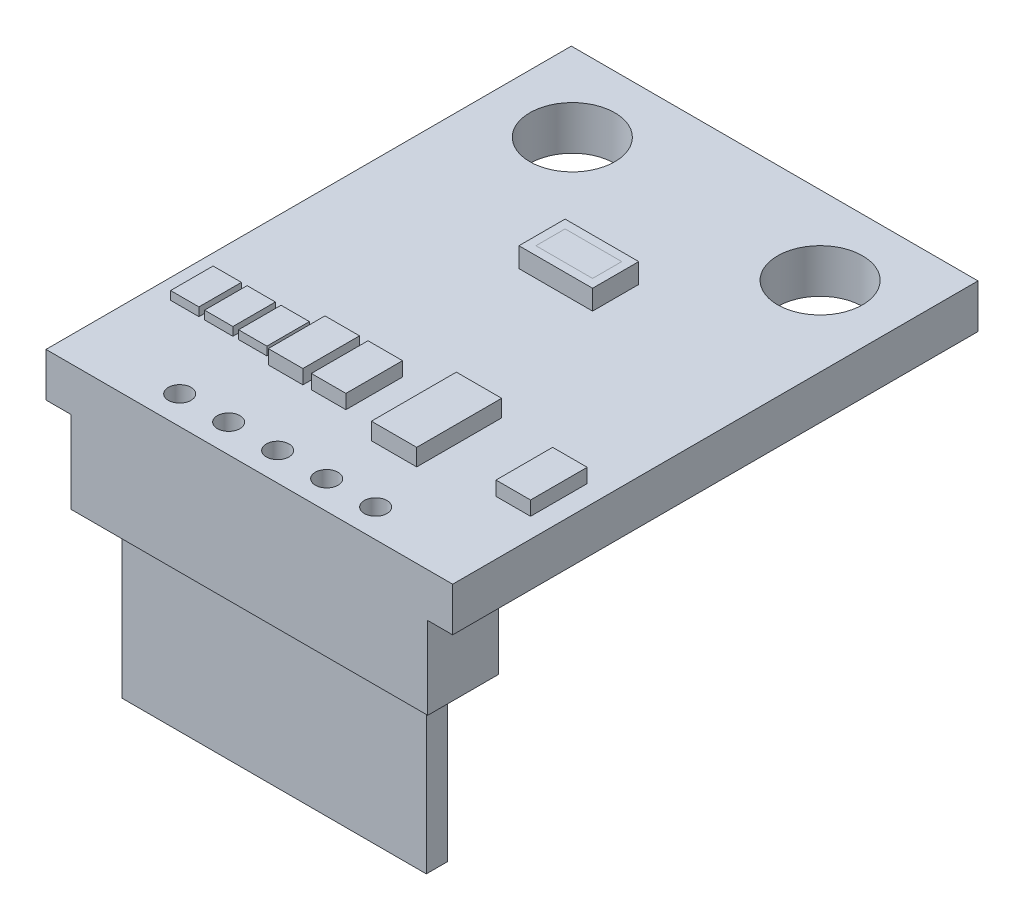
SolidWorks part; units mm, degrees
ref_plane "Front Plane" through (0, 0, 0) normal (0, 0, 1) x (1, 0, 0)
ref_plane "Top Plane" through (0, 0, 0) normal (0, 1, 0) x (1, 0, 0)
ref_plane "Right Plane" through (0, 0, 0) normal (1, 0, 0) x (0, 0, -1)
sketch "Sketch1" plane through (0, 0, 0) normal (0, 1, 0) x (1, 0, 0)
  line L1 (-7.18, -9.275) -> (7.18, -9.275)
  line L2 (-7.18, -9.275) -> (-7.18, 9.275)
  line L3 (-7.18, 9.275) -> (7.18, 9.275)
  line L4 (7.18, -9.275) -> (7.18, 9.275)
  line L5 (-7.18, -9.275) -> (7.18, 9.275) construction
  line L6 (-7.18, 9.275) -> (7.18, -9.275) construction
  point P0 (0, 0)
  dimension "D1" = 14.36
  dimension "D2" = 18.55
extrude "Boss-Extrude1" add sketch "Sketch1" along normal blind 1.55
sketch "Sketch2" plane through (0, 1.55, 0) normal (0, 1, 0) x (1, 0, 0)
  line L0 (-2.875, 6.505) -> (2.875, 6.505) construction
  line L1 (-3.46, -8.275) -> (-1.73, -8.275) construction
  line L2 (7.18, 9.275) -> (-7.18, 9.275) construction
  line L3 (-1.09, -8.275) -> (0.6303, -8.275) construction
  line L4 (0, -8.275) -> (-1.73, -8.275) construction
  line L5 (-7.18, -9.275) -> (7.18, -9.275) construction
  line L6 (0, -8.275) -> (1.73, -8.275) construction
  line L7 (1.73, -8.275) -> (3.46, -8.275) construction
  circle A0 centre (-4.375, 6.505) radius 1.5
  circle A1 centre (4.375, 6.505) radius 1.5
  circle A2 centre (-1.73, -8.275) radius 0.4
  circle A3 centre (1.73, -8.275) radius 0.4
  circle A4 centre (3.46, -8.275) radius 0.4
  circle A5 centre (-3.46, -8.275) radius 0.4
  circle A6 centre (0, -8.275) radius 0.4
  point P6 (0, 6.505)
  point P28 (0, -9.275)
  dimension "D1" = 3
  dimension "D3" = 1.27
  dimension "D4" = 0.6
  dimension "D5" = 0.8
  dimension "D2" = 5.75
  dimension "D6" = 1.73
extrude "Cut-Extrude1" cut sketch "Sketch2" against normal through all
sketch "Sketch5" plane through (0, 1.55, 0) normal (0, 1, 0) x (1, 0, 0)
  line L0 (7.18, 9.275) -> (-7.18, 9.275) construction
  line L1 (-1.3, 1.545) -> (1.3, 1.545)
  line L2 (-1.3, 1.545) -> (-1.3, 3.175)
  line L3 (-1.3, 3.175) -> (1.3, 3.175)
  line L4 (1.3, 1.545) -> (1.3, 3.175)
  line L5 (-1.3, 1.545) -> (1.3, 3.175) construction
  line L6 (-1.3, 3.175) -> (1.3, 1.545) construction
  point P0 (0, 2.36)
  dimension "D1" = 2.6
  dimension "D2" = 1.63
  dimension "D3" = 6.1
extrude "Sensor" add sketch "Sketch5" along normal blind 0.7
sketch "Sketch6" plane through (0, 1.55, 0) normal (0, 1, 0) x (1, 0, 0)
  line L0 (-5.98, -4.825) -> (-3.58, -4.825) construction
  line L1 (-5.48, -5.575) -> (-6.48, -5.575)
  line L2 (-5.48, -5.575) -> (-5.48, -4.075)
  line L3 (-5.48, -4.075) -> (-6.48, -4.075)
  line L4 (-6.48, -5.575) -> (-6.48, -4.075)
  line L5 (-5.48, -5.575) -> (-6.48, -4.075) construction
  line L6 (-5.48, -4.075) -> (-6.48, -5.575) construction
  line L7 (-5.28, -5.575) -> (-4.28, -5.575)
  line L8 (-5.28, -5.575) -> (-5.28, -4.075)
  line L9 (-5.28, -4.075) -> (-4.28, -4.075)
  line L10 (-4.28, -5.575) -> (-4.28, -4.075)
  line L11 (-5.28, -5.575) -> (-4.28, -4.075) construction
  line L12 (-5.28, -4.075) -> (-4.28, -5.575) construction
  line L13 (-4.08, -5.575) -> (-3.08, -5.575)
  line L14 (-4.08, -5.575) -> (-4.08, -4.075)
  line L15 (-4.08, -4.075) -> (-3.08, -4.075)
  line L16 (-3.08, -5.575) -> (-3.08, -4.075)
  line L17 (-4.08, -5.575) -> (-3.08, -4.075) construction
  line L18 (-4.08, -4.075) -> (-3.08, -5.575) construction
  line L19 (-5.48, -4.075) -> (-5.28, -4.075) construction
  line L20 (-4.28, -4.075) -> (-4.08, -4.075) construction
  line L21 (-7.18, 9.275) -> (-7.18, -9.275) construction
  line L22 (-7.18, -9.275) -> (7.18, -9.275) construction
  point P0 (-5.98, -4.825)
  point P5 (-4.78, -4.825)
  point P10 (-3.58, -4.825)
  dimension "D1" = 1
  dimension "D2" = 1.5
  dimension "D3" = 0.7
  dimension "D4" = 3.7
  dimension "D5" = 3.4
extrude "Capacitors1" add sketch "Sketch6" along normal blind 0.3
sketch "Sketch7" plane through (0, 1.55, 0) normal (0, 1, 0) x (1, 0, 0)
  line L0 (-1.56, -3.825) -> (-1.26, -3.825) construction
  line L1 (-2.78, -5.825) -> (-1.56, -5.825)
  line L2 (-2.78, -5.825) -> (-2.78, -3.825)
  line L3 (-2.78, -3.825) -> (-1.56, -3.825)
  line L4 (-1.56, -5.825) -> (-1.56, -3.825)
  line L5 (-2.78, -5.825) -> (-1.56, -3.825) construction
  line L6 (-2.78, -3.825) -> (-1.56, -5.825) construction
  line L7 (-1.26, -5.825) -> (-0.04, -5.825)
  line L8 (-1.26, -5.825) -> (-1.26, -3.825)
  line L9 (-1.26, -3.825) -> (-0.04, -3.825)
  line L10 (-0.04, -5.825) -> (-0.04, -3.825)
  line L11 (-1.26, -5.825) -> (-0.04, -3.825) construction
  line L12 (-1.26, -3.825) -> (-0.04, -5.825) construction
  line L13 (-2.78, -3.825) -> (-3.08, -3.825) construction
  line L14 (-3.08, -4.075) -> (-3.08, -3.825) construction
  line L15 (-2.17, -4.825) -> (-3.08, -4.825) construction
  line L16 (-3.08, -5.575) -> (-3.08, -4.075) construction
  line L17 (7.18, -9.275) -> (7.18, 9.275) construction
  line L18 (5.26, -5.825) -> (6.48, -5.825)
  line L19 (5.26, -5.825) -> (5.26, -3.825)
  line L20 (5.26, -3.825) -> (6.48, -3.825)
  line L21 (6.48, -5.825) -> (6.48, -3.825)
  line L22 (5.26, -5.825) -> (6.48, -3.825) construction
  line L23 (5.26, -3.825) -> (6.48, -5.825) construction
  point P0 (-2.17, -4.825)
  point P5 (-0.65, -4.825)
  point P19 (5.87, -4.825)
  dimension "D1" = 2.74
  dimension "D2" = 0.3
  dimension "D3" = 2
  dimension "D4" = 0.7
extrude "Capacitors2" add sketch "Sketch7" along normal blind 0.5
sketch "Sketch8" plane through (0, 1.55, 0) normal (0, 1, 0) x (1, 0, 0)
  line L0 (5.26, -3.825) -> (5.26, -5.825) construction
  line L1 (1.36, -6.325) -> (2.96, -6.325)
  line L2 (1.36, -6.325) -> (1.36, -3.325)
  line L3 (1.36, -3.325) -> (2.96, -3.325)
  line L4 (2.96, -6.325) -> (2.96, -3.325)
  line L5 (1.36, -6.325) -> (2.96, -3.325) construction
  line L6 (1.36, -3.325) -> (2.96, -6.325) construction
  line L7 (-0.04, -5.825) -> (-0.04, -3.825) construction
  point P0 (2.16, -4.825)
  point P10 (-0.04, -4.825)
  dimension "D1" = 1.6
  dimension "D2" = 3
  dimension "D3" = 2.3
extrude "misc.chip1" add sketch "Sketch8" along normal blind 0.6
sketch "Sketch9" plane through (0, 2.25, 0) normal (0, 1, 0) x (1, 0, 0)
  line L12 (1, 1.845) -> (1, 2.875)
  line L13 (1, 2.875) -> (-1, 2.875)
  line L14 (-1, 2.875) -> (-1, 1.845)
  line L15 (-1, 1.845) -> (1, 1.845)
  line L16 (1, 1.845) -> (1, 2.875)
  line L17 (1, 2.875) -> (-1, 2.875)
  line L18 (-1, 2.875) -> (-1, 1.845)
  line L19 (-1, 1.845) -> (1, 1.845)
  dimension "D1" = 0.3
split line "Split Line1"
sketch "BodyAlignment" plane through (0, 0, 0) normal (0, -1, 0) x (1, 0, 0)
  line L0 (0, -9.275) -> (0, 9.275) construction
  line L1 (7.18, -9.275) -> (-7.18, -9.275) construction
  line L2 (-7.18, 9.275) -> (7.18, 9.275) construction
  line L3 (7.18, 0) -> (-7.18, 0) construction
  line L4 (7.18, 9.275) -> (7.18, -9.275) construction
  line L5 (-7.18, -9.275) -> (-7.18, 9.275) construction
sketch "Sketch10" plane through (0, 0, 0) normal (0, -1, 0) x (1, 0, 0)
  line L0 (3.86, 8.275) -> (-3.86, 8.275) construction
  line L1 (6.3, 6.775) -> (-6.3, 6.775)
  line L2 (6.3, 6.775) -> (6.3, 9.275)
  line L3 (6.3, 9.275) -> (-6.3, 9.275)
  line L4 (-6.3, 6.775) -> (-6.3, 9.275)
  line L6 (-7.18, 9.275) -> (7.18, 9.275) construction
  circle A0 centre (3.46, 8.275) radius 0.4 construction
  circle A1 centre (-3.46, 8.275) radius 0.4 construction
  point P11 (0, 6.775)
  point P12 (0, 8.275)
  point P13 (0, 0)
  point P14 (6.3, 6.393)
  point P15 (6.3, 11.2946)
  point P16 (6.3, 10.2417)
  dimension "D1" = 12.6
  dimension "D2" = 2.5
extrude "Boss-Extrude2" add sketch "Sketch10" along normal blind 2.9
sketch "Sketch12" plane through (0, -2.9, 0) normal (0, -1, 0) x (1, 0, 0)
  line L0 (6.3, 6.775) -> (6.3, 9.275) construction
  line L1 (5.375, 7.65) -> (-5.375, 7.65)
  line L2 (5.375, 7.65) -> (5.375, 8.4)
  line L3 (5.375, 8.4) -> (-5.375, 8.4)
  line L4 (-5.375, 7.65) -> (-5.375, 8.4)
  point P4 (5.375, 8.025)
  point P7 (6.3, 8.025)
  point P8 (0, 7.65)
  dimension "D1" = 0.75
  dimension "D2" = 10.75
extrude "Boss-Extrude3" add sketch "Sketch12" along normal blind 5.75
sketch3d "AlignmentSketch"
  line L0 (1.3, 2.25, -2.36) -> (-1.3, 2.25, -2.36) construction
  line L1 (1.3, 2.25, -1.545) -> (1.3, 2.25, -3.175) construction
  line L2 (-1.3, 2.25, -3.175) -> (-1.3, 2.25, -1.545) construction
  line L3 (0, 2.25, -3.175) -> (0, 2.25, -1.545) construction
  line L4 (1.3, 2.25, -3.175) -> (-1.3, 2.25, -3.175) construction
  line L5 (-1.3, 2.25, -1.545) -> (1.3, 2.25, -1.545) construction
  line L6 (1.3, 2.25, -2.36) -> (1.3, 1.55, -2.36) construction
  line L7 (1.3, 1.55, -1.545) -> (1.3, 1.55, -3.175) construction
  line L8 (0, 2.25, -3.175) -> (0, 1.55, -3.175) construction
  line L9 (1.3, 1.55, -3.175) -> (-1.3, 1.55, -3.175) construction
  line L10 (-1.3, 2.25, -2.36) -> (-1.3, 1.55, -2.36) construction
  line L11 (-1.3, 1.55, -3.175) -> (-1.3, 1.55, -1.545) construction
  line L12 (0, 2.25, -1.545) -> (0, 1.55, -1.545) construction
  line L13 (-1.3, 1.55, -1.545) -> (1.3, 1.55, -1.545) construction
  line L14 (1.3, 1.55, -2.36) -> (7.18, 1.55, -2.36) construction
  line L15 (7.18, 1.55, 9.275) -> (7.18, 1.55, -9.275) construction
  line L16 (7.18, 1.55, -2.36) -> (7.18, 0, -2.36) construction
  line L17 (7.18, 0, 9.275) -> (7.18, 0, -9.275) construction
  line L18 (-1.3, 1.55, -2.36) -> (-7.18, 1.55, -2.36) construction
  line L19 (-7.18, 1.55, -9.275) -> (-7.18, 1.55, 9.275) construction
  line L20 (-7.18, 1.55, -2.36) -> (-7.18, 0, -2.36) construction
  line L21 (-7.18, 0, -9.275) -> (-7.18, 0, 9.275) construction
  line L22 (5.24, 1.55, -2.36) -> (5.24, 0, -2.36) construction
  point P38 (5.24, -2.4186, -2.36)
  dimension "D1" = 1.94
ref_plane "Plane1" through (0, 0, -2.36) normal (0, 0, -1) x (-1, 0, 0)
